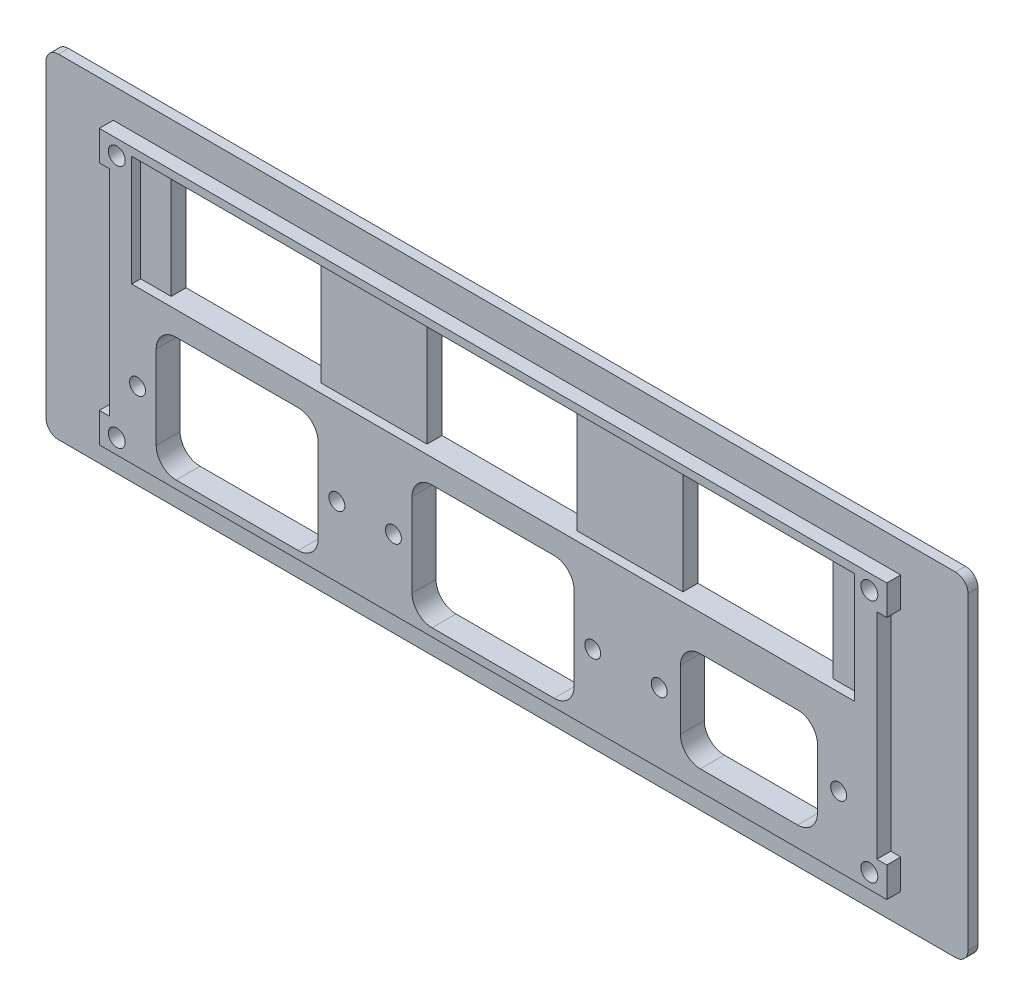
SolidWorks part; units mm, degrees
ref_plane "Přední rovina" through (0, 0, 0) normal (0, 0, 1) x (1, 0, 0)
ref_plane "Horní rovina" through (0, 0, 0) normal (0, 1, 0) x (1, 0, 0)
ref_plane "Pravá rovina" through (0, 0, 0) normal (1, 0, 0) x (0, 0, -1)
sketch "Skica1" plane through (0, 0, 0) normal (0, 0, 1) x (1, 0, 0)
  line L1 (-90, 33.5) -> (90, 33.5)
  line L2 (-92.5, 31) -> (-92.5, -31)
  line L3 (-90, -33.5) -> (90, -33.5)
  line L4 (92.5, 31) -> (92.5, -31)
  line L5 (-92.5, 33.5) -> (92.5, -33.5) construction
  line L6 (-92.5, -33.5) -> (92.5, 33.5) construction
  arc A0 (-92.5, -31) -> (-90, -33.5) centre (-90, -31) ccw
  arc A1 (90, -33.5) -> (92.5, -31) centre (90, -31) ccw
  arc A2 (90, 33.5) -> (92.5, 31) centre (90, 31) cw
  arc A3 (-90, 33.5) -> (-92.5, 31) centre (-90, 31) ccw
  point P0 (0, 0)
  dimension "D3" = 2.5
  dimension "D1" = 185
  dimension "D2" = 67
extrude "Přidat vysunutím1" add sketch "Skica1" along normal blind 2
sketch "Skica2" plane through (0, 0, 2) normal (0, 0, 1) x (1, 0, 0)
  line L1 (-77, 27.5) -> (77, 27.5)
  line L2 (-77, 27.5) -> (-77, -27.5)
  line L3 (-77, -27.5) -> (77, -27.5)
  line L4 (77, 27.5) -> (77, -27.5)
  line L5 (-77, 27.5) -> (77, -27.5) construction
  line L6 (-77, -27.5) -> (77, 27.5) construction
  point P0 (0, 0)
  dimension "D1" = 154
  dimension "D2" = 55
extrude "Přidat vysunutím2" add sketch "Skica2" along normal blind 2.8
sketch "Skica3" plane through (0, 0, 4.8) normal (0, 0, 1) x (1, 0, 0)
  line L0 (-77, -13.5) -> (77, -13.5)
  line L1 (-77, 27.5) -> (-77, -27.5) construction
  line L2 (77, -27.5) -> (77, 27.5) construction
  line L3 (-77, 14.8) -> (77, 14.8)
  line L4 (-39.09, -1.1) -> (-63.59, -1.1)
  line L5 (-35.09, -5.1) -> (-35.09, -21.9)
  line L6 (-39.09, -25.9) -> (-63.59, -25.9)
  line L7 (-67.59, -5.1) -> (-67.59, -21.9)
  line L8 (-35.09, -1.1) -> (-67.59, -25.9) construction
  line L9 (-35.09, -25.9) -> (-67.59, -1.1) construction
  line L10 (12.25, -1.1) -> (-12.25, -1.1)
  line L11 (16.25, -5.1) -> (16.25, -21.9)
  line L12 (12.25, -25.9) -> (-12.25, -25.9)
  line L13 (-16.25, -5.1) -> (-16.25, -21.9)
  line L14 (16.25, -1.1) -> (-16.25, -25.9) construction
  line L15 (16.25, -25.9) -> (-16.25, -1.1) construction
  line L16 (61.09, -3.5) -> (41.59, -3.5)
  line L17 (65.09, -7.5) -> (65.09, -19.5)
  line L18 (61.09, -23.5) -> (41.59, -23.5)
  line L19 (37.59, -7.5) -> (37.59, -19.5)
  line L20 (65.09, -3.5) -> (37.59, -23.5) construction
  line L21 (65.09, -23.5) -> (37.59, -3.5) construction
  line L22 (-51.34, -13.5) -> (-51.34, 14.8)
  line L23 (0, -13.5) -> (0, 19.2642)
  line L24 (51.34, -13.5) -> (51.34, 14.8)
  line L26 (-36.29, 25.9) -> (-66.39, 25.9)
  line L27 (-36.29, 25.9) -> (-36.29, 3.7)
  line L28 (-36.29, 3.7) -> (-66.39, 3.7)
  line L29 (-66.39, 25.9) -> (-66.39, 3.7)
  line L30 (-36.29, 25.9) -> (-66.39, 3.7) construction
  line L31 (-36.29, 3.7) -> (-66.39, 25.9) construction
  line L32 (15.05, 25.9) -> (-15.05, 25.9)
  line L33 (15.05, 25.9) -> (15.05, 3.7)
  line L34 (15.05, 3.7) -> (-15.05, 3.7)
  line L35 (-15.05, 25.9) -> (-15.05, 3.7)
  line L36 (15.05, 25.9) -> (-15.05, 3.7) construction
  line L37 (15.05, 3.7) -> (-15.05, 25.9) construction
  line L38 (66.39, 25.9) -> (36.29, 25.9)
  line L39 (66.39, 25.9) -> (66.39, 3.7)
  line L40 (66.39, 3.7) -> (36.29, 3.7)
  line L41 (36.29, 25.9) -> (36.29, 3.7)
  line L42 (66.39, 25.9) -> (36.29, 3.7) construction
  line L43 (66.39, 3.7) -> (36.29, 25.9) construction
  arc A0 (41.59, -23.5) -> (37.59, -19.5) centre (41.59, -19.5) cw
  arc A1 (65.09, -19.5) -> (61.09, -23.5) centre (61.09, -19.5) cw
  arc A2 (61.09, -3.5) -> (65.09, -7.5) centre (61.09, -7.5) cw
  arc A3 (41.59, -3.5) -> (37.59, -7.5) centre (41.59, -7.5) ccw
  arc A4 (-12.25, -25.9) -> (-16.25, -21.9) centre (-12.25, -21.9) cw
  arc A5 (16.25, -21.9) -> (12.25, -25.9) centre (12.25, -21.9) cw
  arc A6 (12.25, -1.1) -> (16.25, -5.1) centre (12.25, -5.1) cw
  arc A7 (-12.25, -1.1) -> (-16.25, -5.1) centre (-12.25, -5.1) ccw
  arc A8 (-63.59, -25.9) -> (-67.59, -21.9) centre (-63.59, -21.9) cw
  arc A9 (-35.09, -21.9) -> (-39.09, -25.9) centre (-39.09, -21.9) cw
  arc A10 (-39.09, -1.1) -> (-35.09, -5.1) centre (-39.09, -5.1) cw
  arc A11 (-63.59, -1.1) -> (-67.59, -5.1) centre (-63.59, -5.1) ccw
  arc A12 (12.25, -1.1) -> (16.25, -5.1) centre (12.25, -5.1) cw
  arc A13 (12.25, -1.1) -> (16.25, -5.1) centre (12.25, -5.1) cw
  arc A14 (12.25, -1.1) -> (16.25, -5.1) centre (12.25, -5.1) cw
  circle A15 centre (-20, -13.5) radius 1.6
  circle A16 centre (20, -13.5) radius 1.6
  circle A17 centre (33.34, -13.5) radius 1.6
  circle A18 centre (69.34, -13.5) radius 1.6
  circle A19 centre (-31.34, -13.5) radius 1.6
  circle A20 centre (-71.34, -13.5) radius 1.6
  point P6 (-51.34, -13.5)
  point P7 (0, -13.5)
  point P9 (51.34, -13.5)
  point P10 (-51.34, -13.5)
  point P15 (0, -13.5)
  point P20 (51.34, -13.5)
  point P90 (0, 14.8)
  dimension "D10" = 4
  dimension "D11" = 4
  dimension "D12" = 4
  dimension "D13" = 4
  dimension "D14" = 3.2
  dimension "D1" = 14
  dimension "D2" = 25.66
  dimension "D3" = 25.66
  dimension "D4" = 32.5
  dimension "D5" = 24.8
  dimension "D6" = 32.5
  dimension "D7" = 24.8
  dimension "D8" = 27.5
  dimension "D9" = 20
  dimension "D15" = 20
  dimension "D16" = 20
  dimension "D17" = 18
  dimension "D18" = 18
  dimension "D19" = 20
  dimension "D20" = 20
  dimension "D21" = 12.7
  dimension "D22" = 30.1
  dimension "D23" = 22.2
extrude "Odebrat vysunutím1" cut sketch "Skica3" against normal through all contours L26 L29 L28 L27 | L32 L35 L34 L33 | L38 L41 L40 L39 | L4 A11 L7 A8 L6 A9 L5 A10 | L10 A7 L13 A4 L12 A5 L11 A14 | L16 A3 L19 A0 L18 A1 L17 A2 | A20 | A19 | A15 | A16 | A17 | A18
sketch "Skica4" plane through (0, 0, 4.8) normal (0, 0, 1) x (1, 0, 0)
  line L0 (0, 3.7) -> (0, 25.9)
  line L1 (15.05, 3.7) -> (-15.05, 3.7) construction
  line L2 (15.05, 25.9) -> (-15.05, 25.9) construction
  line L4 (72.5, 25.9) -> (-72.5, 25.9)
  line L5 (72.5, 25.9) -> (72.5, 3.7)
  line L6 (72.5, 3.7) -> (-72.5, 3.7)
  line L7 (-72.5, 25.9) -> (-72.5, 3.7)
  line L8 (72.5, 25.9) -> (-72.5, 3.7) construction
  line L9 (72.5, 3.7) -> (-72.5, 25.9) construction
  point P6 (0, 14.8)
  dimension "D1" = 145
extrude "Odebrat vysunutím2" cut sketch "Skica4" against normal blind 1.8 contours L4 L7 L6 L5
sketch "Skica5" plane through (0, 0, 2) normal (0, 0, 1) x (1, 0, 0)
  line L0 (-77, -27.5) -> (-79, -27.5)
  line L1 (-79, -27.5) -> (-79, -21.5)
  line L2 (-79, -21.5) -> (-77, -21.5)
  line L3 (-77, 27.5) -> (-77, -27.5) construction
  line L4 (0, 0) -> (-21.4153, 0)
  line L5 (0, 0) -> (0, -11.6783)
  line L6 (-77, 27.5) -> (-79, 27.5)
  line L7 (-79, 27.5) -> (-79, 21.5)
  line L8 (-79, 21.5) -> (-77, 21.5)
  line L9 (77, 27.5) -> (79, 27.5)
  line L10 (79, 27.5) -> (79, 21.5)
  line L11 (79, 21.5) -> (77, 21.5)
  line L12 (79, -21.5) -> (77, -21.5)
  line L13 (79, -27.5) -> (79, -21.5)
  line L14 (77, -27.5) -> (79, -27.5)
  line M18 (77, 27.5) -> (77, -27.5)
  line M20 (-77, -27.5) -> (-77, 27.5)
  dimension "D1" = 2
  dimension "D2" = 6
extrude "Přidat vysunutím3" add sketch "Skica5" along direction (0, 0, 1) on the side of the normal up to surface (2.8 mm away) contours L7 L8 L6 M20 | L2 L1 L0 M20 | L14 L13 L12 M18 | L11 L10 L9 M18
sketch "Skica6" plane through (0, 0, 0) normal (0, 0, -1) x (-1, 0, 0)
  line L1 (-75.5, 24.5) -> (75.5, 24.5)
  line L2 (-75.5, 24.5) -> (-75.5, -24.5)
  line L3 (-75.5, -24.5) -> (75.5, -24.5)
  line L4 (75.5, 24.5) -> (75.5, -24.5)
  line L5 (-75.5, 24.5) -> (75.5, -24.5) construction
  line L6 (-75.5, -24.5) -> (75.5, 24.5) construction
  point P0 (0, 0)
  dimension "D1" = 49
  dimension "D2" = 151
hole_wizard "Kuželové zahloubení pro M3 šroubu se zápustnou hlavou plochou1" positions "Skica7" profile "Skica8" countersink size "M3" standard "DIN" end condition through all
sketch "Skica7" plane through (0, 0, 0) normal (0, 0, -1) x (-1, 0, 0)
  point P0 (-75.5, -24.5)
  point P3 (-75.5, 24.5)
  point P6 (75.5, 24.5)
  point P9 (75.5, -24.5)
sketch "Skica8" plane through (75.5, -24.5, 0) normal (1, 0, 0) x (0, 1, 0)
  line L0 (0, 0) -> (0, 4.8)
  line L1 (0, 4.8) -> (1.7, 4.8)
  line L2 (1.7, 4.8) -> (1.7, 1.45)
  line L3 (1.7, 1.45) -> (3.15, 0)
  line L5 (3.15, 0) -> (0, 0)
  line L6 (-1.7, 1.45) -> (-3.15, 0) construction
  line L11 (0, -6.35) -> (0, 107.95) construction
  dimension "Průměr díry skrz" = 3.4
  dimension "Hloubka díry skrz" = 4.8
  dimension "Průměr blíz. kuž. zahloubení" = 6.3
  dimension "Úhel blíz. kuž. zahloubení" = 90
